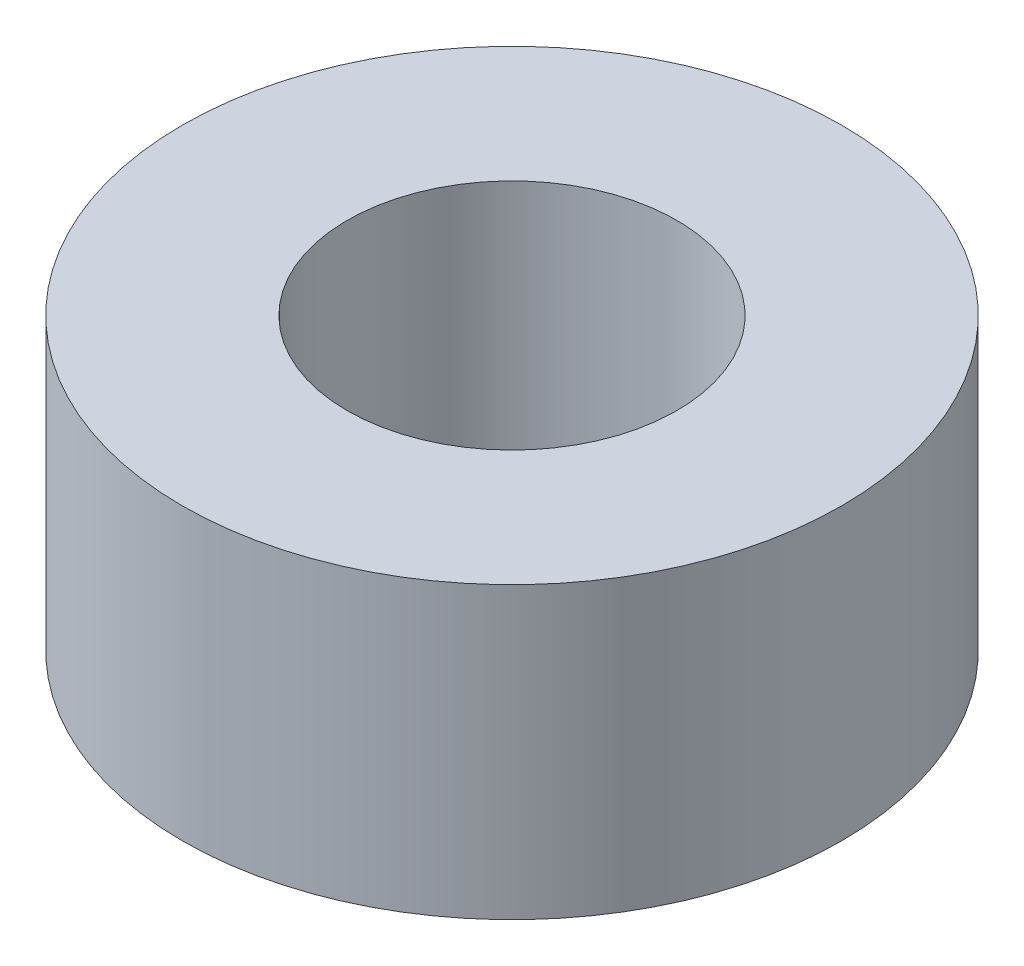
SolidWorks part; units mm, degrees
material "PVC Rigid"
ref_plane "Front Plane" through (0, 0, 0) normal (0, 0, 1) x (1, 0, 0)
ref_plane "Top Plane" through (0, 0, 0) normal (0, 1, 0) x (1, 0, 0)
ref_plane "Right Plane" through (0, 0, 0) normal (1, 0, 0) x (0, 0, -1)
sketch "Sketch1" plane through (0, 0, 0) normal (0, 1, 0) x (1, 0, 0)
  circle A0 centre (0, 0) radius 6.35
  circle A1 centre (0, 0) radius 3.175
  dimension "D1" = 12.7
  dimension "D2" = 6.35
extrude "Boss-Extrude1" add sketch "Sketch1" along normal blind 5.588
